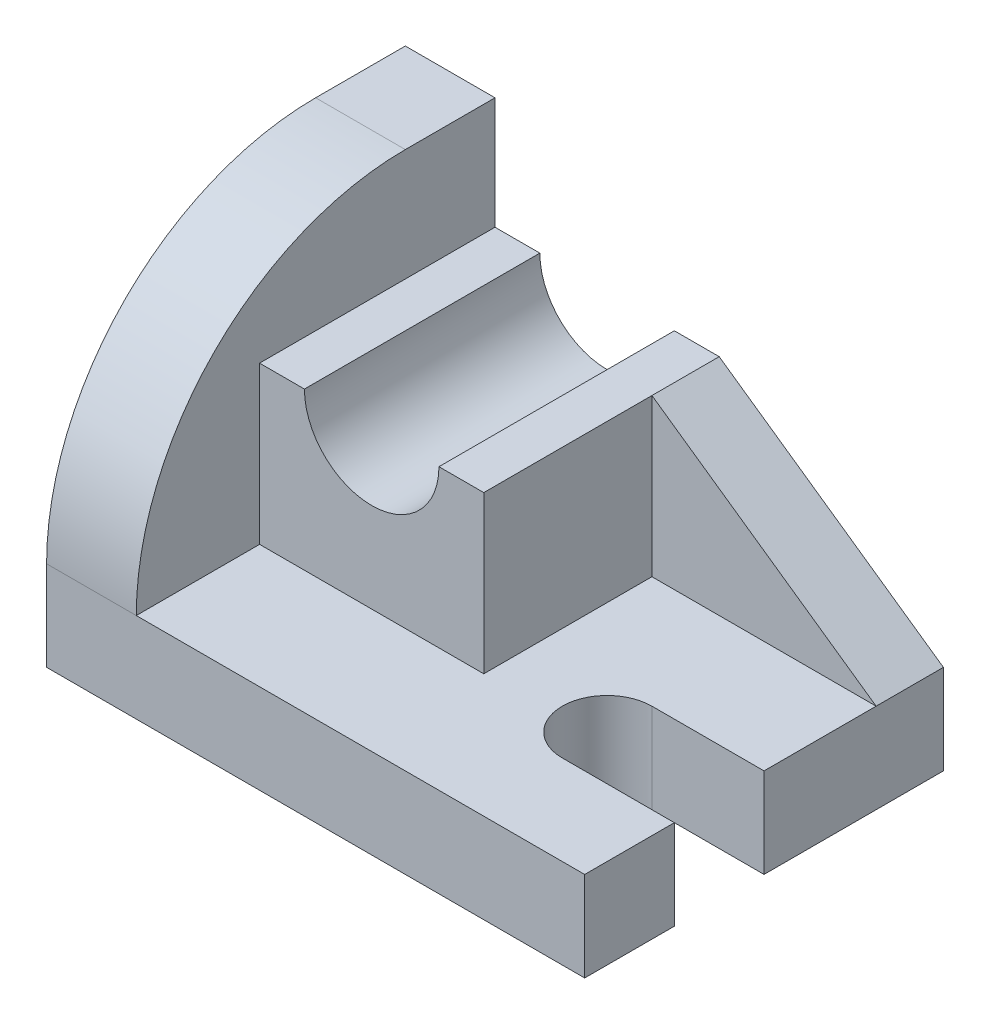
SolidWorks part; units mm, degrees
ref_plane "Front Plane" through (0, 0, 0) normal (0, 0, 1) x (1, 0, 0)
ref_plane "Top Plane" through (0, 0, 0) normal (0, 1, 0) x (1, 0, 0)
ref_plane "Right Plane" through (0, 0, 0) normal (1, 0, 0) x (0, 0, -1)
sketch "Sketch1" plane through (0, 0, 0) normal (1, 0, 0) x (0, 0, -1)
  line L1 (-32, 8) -> (32, 8)
  line L2 (-32, 8) -> (-32, -8)
  line L3 (-32, -8) -> (32, -8)
  line L4 (32, 8) -> (32, -8)
  line L5 (-32, 8) -> (32, -8) construction
  line L6 (-32, -8) -> (32, 8) construction
  point P0 (0, 0)
extrude "Boss-Extrude1" add sketch "Sketch1" against normal blind 96
sketch "Sketch3" plane through (0, 8, 0) normal (0, 1, 0) x (1, 0, 0)
  line L0 (0, -32) -> (0, -16) construction
  line L1 (0, 32) -> (0, -32) construction
  line L2 (0, -16) -> (-20, -16) construction
  line L3 (-20, -16) -> (-20, -8) construction
  line L4 (-20, 0) -> (0, 0)
  line L5 (0, 0) -> (0, -16)
  line L6 (0, -16) -> (-20, -16)
  arc A0 (-20, -16) -> (-20, 0) centre (-20, -8) cw
extrude "Cut-Extrude1" cut sketch "Sketch3" against normal through all
sketch "Sketch4" plane through (0, 0, -32) normal (0, 0, -1) x (-1, 0, 0)
  line L0 (0, 8) -> (40, 8)
  line L1 (96, 8) -> (0, 8) construction
  line L2 (40, 8) -> (40, 36)
  line L3 (40, 36) -> (0, 8)
extrude "Boss-Extrude2" add sketch "Sketch4" against normal blind 12
sketch "Sketch5" plane through (0, 8, 0) normal (0, 1, 0) x (1, 0, 0)
  line L1 (-40, 32) -> (-80, 32)
  line L2 (-40, 32) -> (-40, -10)
  line L3 (-40, -10) -> (-80, -10)
  line L4 (-80, 32) -> (-80, -10)
extrude "Boss-Extrude3" add sketch "Sketch5" along normal blind 28
sketch "Sketch11" plane through (0, 8, 0) normal (0, 1, 0) x (1, 0, 0)
  line L0 (-96, -32) -> (0, -32) construction
  line L1 (-96, 32) -> (-80, 32)
  line L2 (-96, 32) -> (-96, -32)
  line L3 (-96, -32) -> (-80, -32)
  line L4 (-80, 32) -> (-80, -32)
extrude "Boss-Extrude6" add sketch "Sketch11" along normal blind 48
fillet "Fillet2" radius 48 1 edges at (-88, 56, 32)
sketch "Sketch13" plane through (0, 0, 10) normal (0, 0, 1) x (1, 0, 0)
  line L0 (-80, 36) -> (-40, 36) construction
  line L1 (-48, 36) -> (-72, 36)
  arc A0 (-72, 36) -> (-48, 36) centre (-60, 36) ccw
extrude "Cut-Extrude4" cut sketch "Sketch13" against normal through all
